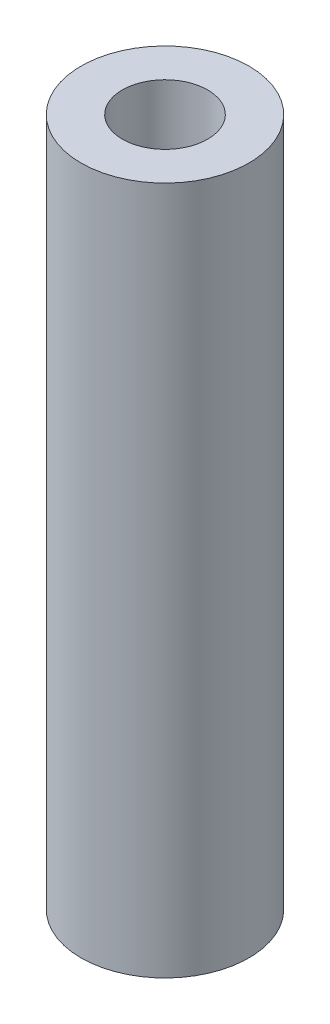
SolidWorks part; units mm, degrees
ref_plane "Front Plane" through (0, 0, 0) normal (0, 0, 1) x (1, 0, 0)
ref_plane "Top Plane" through (0, 0, 0) normal (0, 1, 0) x (1, 0, 0)
ref_plane "Right Plane" through (0, 0, 0) normal (1, 0, 0) x (0, 0, -1)
sketch "Sketch1" plane through (0, 0, 0) normal (0, 1, 0) x (1, 0, 0)
  circle A0 centre (0, 0) radius 1.55
  circle A1 centre (0, 0) radius 3.05
  dimension "D1" = 3.1
  dimension "D2" = 1.5
extrude "Boss-Extrude1" add sketch "Sketch1" along normal blind 25
